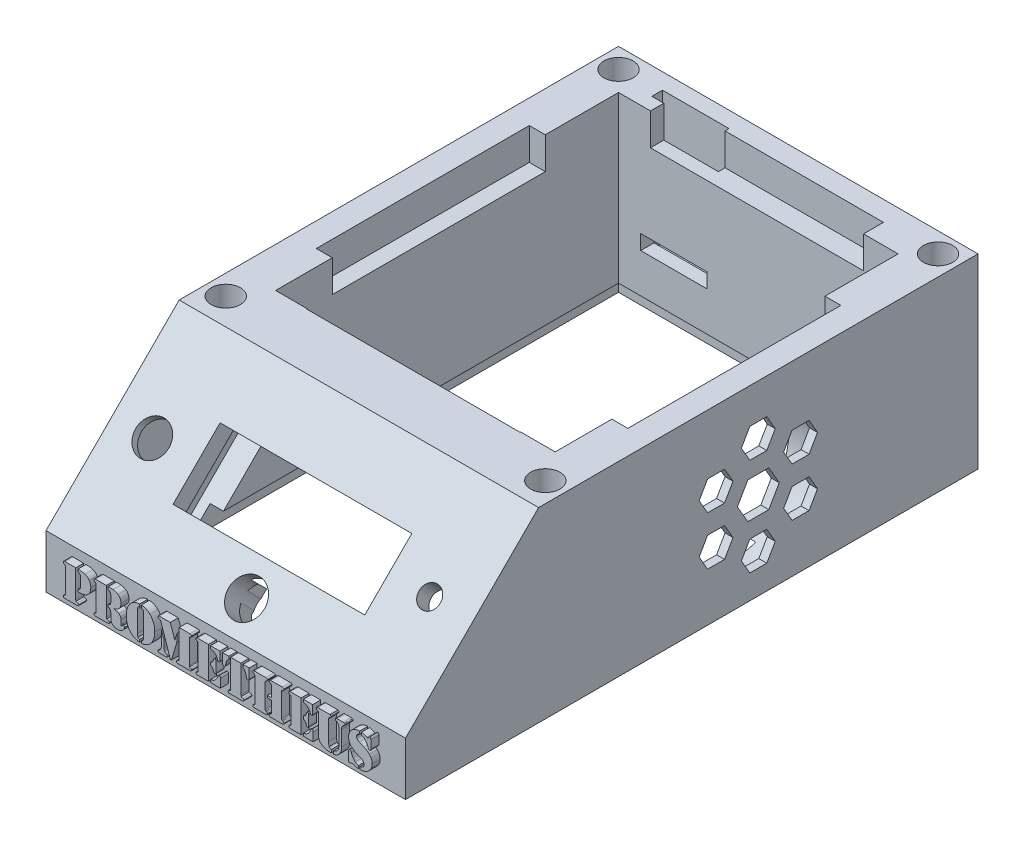
SolidWorks part; units mm, degrees
ref_plane "Front Plane" through (0, 0, 0) normal (0, 0, 1) x (1, 0, 0)
ref_plane "Top Plane" through (0, 0, 0) normal (0, 1, 0) x (1, 0, 0)
ref_plane "Right Plane" through (0, 0, 0) normal (1, 0, 0) x (0, 0, -1)
sketch "Sketch1" plane through (0, 0, 0) normal (0, 1, 0) x (1, 0, 0)
  line L1 (-67.5, -107.5) -> (67.5, -107.5)
  line L2 (-67.5, -107.5) -> (-67.5, 107.5)
  line L3 (-67.5, 107.5) -> (67.5, 107.5)
  line L4 (67.5, -107.5) -> (67.5, 107.5)
  line L5 (-67.5, -107.5) -> (67.5, 107.5) construction
  line L6 (-67.5, 107.5) -> (67.5, -107.5) construction
  point P0 (0, 0)
  dimension "D1" = 135
  dimension "D2" = 215
extrude "Boss-Extrude1" add sketch "Sketch1" along normal blind 70
chamfer "Chamfer1" distance 50 angle 45 1 edges at (0, 70, 107.5)
shell "Shell1" thickness 15
sketch "Sketch2" plane through (0, 0, 0) normal (0, -1, 0) x (-1, 0, 0)
  line L1 (52.5, -91.2868) -> (-52.5, -91.2868)
  line L2 (52.5, -91.2868) -> (52.5, 92.5)
  line L3 (52.5, 92.5) -> (-52.5, 92.5)
  line L4 (-52.5, -91.2868) -> (-52.5, 92.5)
extrude "Cut-Extrude1" cut sketch "Sketch2" against normal blind 15
sketch "Sketch4" plane through (0, 63.75, 63.75) normal (0, 0.7071, 0.7071) x (1, 0, 0)
  line L0 (0, 8.8388) -> (0, -26.4612) construction
  line L1 (-67.5, 8.8388) -> (67.5, 8.8388) construction
  line L2 (0, -26.4612) -> (-67.5, -26.4612) construction
  line L3 (-67.5, -61.8718) -> (-67.5, 8.8388) construction
  line L5 (-36, -13.9612) -> (36, -13.9612)
  line L6 (-36, -13.9612) -> (-36, -38.9612)
  line L7 (-36, -38.9612) -> (36, -38.9612)
  line L8 (36, -13.9612) -> (36, -38.9612)
  line L9 (-36, -13.9612) -> (36, -38.9612) construction
  line L10 (-36, -38.9612) -> (36, -13.9612) construction
  dimension "D1" = 72
  dimension "D2" = 25
extrude "Cut-Extrude2" cut sketch "Sketch4" against normal blind 4.5
sketch "Sketch5" plane through (0, 70, 0) normal (0, 1, 0) x (1, 0, 0)
  line L0 (-60, 107.5) -> (-60, 100) construction
  line L1 (67.5, 107.5) -> (-67.5, 107.5) construction
  line L2 (-60, 100) -> (-67.5, 100) construction
  line L3 (-67.5, 107.5) -> (-67.5, -57.5) construction
  circle A0 centre (-60, 100) radius 5.5
extrude "Cut-Extrude3" cut sketch "Sketch5" against normal blind 15
sketch "Sketch6" plane through (0, 70, 0) normal (0, 1, 0) x (1, 0, 0)
  line L0 (60, 107.5) -> (60, 100) construction
  line L1 (67.5, 107.5) -> (-67.5, 107.5) construction
  line L2 (60, 100) -> (67.5, 100) construction
  line L3 (67.5, -57.5) -> (67.5, 107.5) construction
  circle A0 centre (60, 100) radius 5.5
extrude "Cut-Extrude4" cut sketch "Sketch6" against normal blind 15
sketch "Sketch7" plane through (0, 70, 0) normal (0, 1, 0) x (1, 0, 0)
  line L0 (-67.5, -47.5) -> (-60, -47.5) construction
  line L1 (-67.5, 107.5) -> (-67.5, -57.5) construction
  line L2 (-60, -47.5) -> (-60, -57.5) construction
  line L3 (-67.5, -57.5) -> (67.5, -57.5) construction
  circle A0 centre (-60, -47.5) radius 5.5
extrude "Cut-Extrude5" cut sketch "Sketch7" against normal blind 15
sketch "Sketch8" plane through (0, 70, 0) normal (0, 1, 0) x (1, 0, 0)
  line L0 (67.5, -47.5) -> (60, -47.5) construction
  line L1 (67.5, -57.5) -> (67.5, 107.5) construction
  line L2 (60, -47.5) -> (60, -57.5) construction
  line L3 (-67.5, -57.5) -> (67.5, -57.5) construction
  circle A0 centre (60, -47.5) radius 5.5
extrude "Cut-Extrude6" cut sketch "Sketch8" against normal blind 15
sketch "Sketch9" plane through (0, 63.75, 63.75) normal (0, 0.7071, 0.7071) x (1, 0, 0)
  line L0 (-52.5796, 8.8388) -> (-52.5796, -26.5112) construction
  line L1 (-67.5, 8.8388) -> (67.5, 8.8388) construction
  line L2 (-52.5796, -26.5112) -> (-67.5, -26.5112) construction
  line L3 (-67.5, -61.8718) -> (-67.5, 8.8388) construction
  circle A0 centre (-52.5796, -26.5112) radius 6.25
extrude "Cut-Extrude7" cut sketch "Sketch9" against normal blind 20
sketch "Sketch10" plane through (0, 53.1434, 53.1434) normal (0, -0.7071, -0.7071) x (1, 0, 0)
  line L1 (-61.0796, 44.0112) -> (-44.0796, 44.0112)
  line L2 (-61.0796, 44.0112) -> (-61.0796, 9.0112)
  line L3 (-61.0796, 9.0112) -> (-44.0796, 9.0112)
  line L4 (-44.0796, 44.0112) -> (-44.0796, 9.0112)
  line L5 (-61.0796, 44.0112) -> (-44.0796, 9.0112) construction
  line L6 (-61.0796, 9.0112) -> (-44.0796, 44.0112) construction
  point P0 (-52.5796, 26.5112)
  dimension "D1" = 17
  dimension "D2" = 35
extrude "Cut-Extrude8" cut sketch "Sketch10" along normal blind 30 and the other way blind 12
sketch "Sketch11" plane through (0, 63.75, 63.75) normal (0, 0.7071, 0.7071) x (1, 0, 0)
  line L0 (51.3456, 8.8388) -> (51.3456, -26.1612) construction
  line L1 (-67.5, 8.8388) -> (67.5, 8.8388) construction
  line L2 (51.3456, -26.1612) -> (67.5, -26.1612) construction
  line L3 (67.5, 8.8388) -> (67.5, -61.8718) construction
  circle A0 centre (51.3456, -26.1612) radius 4
extrude "Cut-Extrude9" cut sketch "Sketch11" against normal blind 20
sketch "Sketch13" plane through (0, 53.1434, 53.1434) normal (0, -0.7071, -0.7071) x (1, 0, 0)
  circle A0 centre (51.3456, 26.1612) radius 10
extrude "Cut-Extrude10" cut sketch "Sketch13" along normal blind 10 and the other way blind 8.5
sketch "Sketch16" plane through (0, 53.1434, 53.1434) normal (0, -0.7071, -0.7071) x (1, 0, 0)
  line L17 (-43, 45.9612) -> (-43, 6.9612)
  line L18 (43, 45.9612) -> (-43, 45.9612)
  line L19 (43, 6.9612) -> (43, 45.9612)
  line L20 (-43, 6.9612) -> (43, 6.9612)
  line L21 (-43, 45.9612) -> (-43, 6.9612)
  line L22 (43, 45.9612) -> (-43, 45.9612)
  line L23 (43, 6.9612) -> (43, 45.9612)
  line L24 (-43, 6.9612) -> (43, 6.9612)
  dimension "D1" = 7
extrude "Cut-Extrude13" cut sketch "Sketch16" against normal blind 11
sketch "Sketch20" plane through (0, 53.1434, 53.1434) normal (0, -0.7071, -0.7071) x (-1, 0, 0)
  line L1 (-61.3456, -26.1612) -> (-43, -26.1612)
  line L2 (-61.3456, -26.1612) -> (-61.3456, -0.9057)
  line L3 (-61.3456, -0.9057) -> (-43, -0.9057)
  line L4 (-43, -26.1612) -> (-43, -0.9057)
  arc A0 (-52.5, -16.228) -> (-52.5, -36.0943) centre (-51.3456, -26.1612) ccw construction
extrude "Cut-Extrude14" cut sketch "Sketch20" against normal blind 8.5
sketch "Sketch21" plane through (0, 70, 0) normal (0, 1, 0) x (1, 0, 0)
  line L0 (0, 107.5) -> (0, 25) construction
  line L1 (67.5, 107.5) -> (-67.5, 107.5) construction
  line L2 (0, 25) -> (-67.5, 25) construction
  line L3 (-67.5, 107.5) -> (-67.5, -57.5) construction
  line L5 (-58.5, 65) -> (58.5, 65)
  line L6 (-58.5, 65) -> (-58.5, -15)
  line L7 (-58.5, -15) -> (58.5, -15)
  line L8 (58.5, 65) -> (58.5, -15)
  line L9 (-58.5, 65) -> (58.5, -15) construction
  line L10 (-58.5, -15) -> (58.5, 65) construction
  dimension "D1" = 117
  dimension "D2" = 80
extrude "Cut-Extrude15" cut sketch "Sketch21" against normal blind 12
sketch "Sketch22" plane through (0, 70, 0) normal (0, 1, 0) x (1, 0, 0)
  line L0 (-0.5, 107.5) -> (-0.5, 31.75) construction
  line L1 (67.5, 107.5) -> (-67.5, 107.5) construction
  line L2 (-0.5, 31.75) -> (-67.5, 31.75) construction
  line L3 (-67.5, 107.5) -> (-67.5, -57.5) construction
  line L5 (-40.5, 100) -> (39.5, 100)
  line L6 (-40.5, 100) -> (-40.5, -36.5)
  line L7 (-40.5, -36.5) -> (39.5, -36.5)
  line L8 (39.5, 100) -> (39.5, -36.5)
  line L9 (-40.5, 100) -> (39.5, -36.5) construction
  line L10 (-40.5, -36.5) -> (39.5, 100) construction
  dimension "D1" = 136.5
  dimension "D2" = 80
extrude "Cut-Extrude16" cut sketch "Sketch22" against normal blind 12
sketch "Sketch25" plane through (0, 0, 107.5) normal (0, 0, 1) x (1, 0, 0)
  line L0 (-67.5, 5.1237) -> (8.0252, 5.1237) construction
  line L1 (-67.5, 20) -> (-67.5, 0) construction
  line L2 (8.0252, 5.1237) -> (58.0252, 5.1237) construction
  line L3 (58.0252, 5.1237) -> (58.0252, 20) construction
  line L4 (67.5, 20) -> (-67.5, 20) construction
  text T0 "prometheus" font "Stencil" height 12
extrude "Boss-Extrude2" add sketch "Sketch25" along normal blind 3
sketch "Sketch26" plane through (0, 70, 0) normal (0, 1, 0) x (1, 0, 0)
  line L0 (-32.5, 107.5) -> (-32.5, 99.5) construction
  line L1 (67.5, 107.5) -> (-67.5, 107.5) construction
  line L2 (-32.5, 99.5) -> (-67.5, 99.5) construction
  line L3 (-67.5, 107.5) -> (-67.5, -57.5) construction
  line L5 (-45, 97.5) -> (-20, 97.5)
  line L6 (-45, 97.5) -> (-45, 101.5)
  line L7 (-45, 101.5) -> (-20, 101.5)
  line L8 (-20, 97.5) -> (-20, 101.5)
  line L9 (-45, 97.5) -> (-20, 101.5) construction
  line L10 (-45, 101.5) -> (-20, 97.5) construction
  dimension "D1" = 25
  dimension "D2" = 4
extrude "Cut-Extrude17" cut sketch "Sketch26" against normal blind 50
sketch "Sketch27" plane through (0, 0, -92.5) normal (0, 0, 1) x (1, 0, 0)
  line L1 (-44.1692, 22.7377) -> (-19.2485, 22.7377)
  line L2 (-44.1692, 22.7377) -> (-44.1692, 28.2929)
  line L3 (-44.1692, 28.2929) -> (-19.2485, 28.2929)
  line L4 (-19.2485, 22.7377) -> (-19.2485, 28.2929)
extrude "Cut-Extrude18" cut sketch "Sketch27" against normal blind 5
sketch "Sketch28" plane through (0, 63.75, 63.75) normal (0, 0.7071, 0.7071) x (1, 0, 0)
  line L0 (0, -39.7138) -> (0, -50.8138) construction
  circle A0 centre (0, -50.8138) radius 6.75
extrude "Cut-Extrude19" cut sketch "Sketch28" against normal blind 30
sketch "Sketch29" plane through (0, 53.1434, 53.1434) normal (0, -0.7071, -0.7071) x (1, 0, 0)
  line L1 (-6.5, 57.3138) -> (6.5, 57.3138)
  line L2 (-6.5, 57.3138) -> (-6.5, 44.3138)
  line L3 (-6.5, 44.3138) -> (6.5, 44.3138)
  line L4 (6.5, 57.3138) -> (6.5, 44.3138)
  line L5 (-6.5, 57.3138) -> (6.5, 44.3138) construction
  line L6 (-6.5, 44.3138) -> (6.5, 57.3138) construction
  point P0 (0, 50.8138)
  dimension "D1" = 13
  dimension "D2" = 13
extrude "Cut-Extrude20" cut sketch "Sketch29" against normal blind 7 and the other way blind 10
sketch "Sketch30" plane through (0, 59.1538, 59.1538) normal (0, -0.7071, -0.7071) x (1, 0, 0)
  line L1 (43, 6.9612) -> (61.3456, 6.9612)
  line L2 (43, 6.9612) -> (43, 36.9612)
  line L3 (43, 36.9612) -> (61.3456, 36.9612)
  line L4 (61.3456, 6.9612) -> (61.3456, 36.9612)
  dimension "D1" = 30
  dimension "D2" = 18.3456
extrude "Cut-Extrude21" cut sketch "Sketch30" along normal blind 35
sketch "Sketch31" plane through (0, 60.9216, 60.9216) normal (0, -0.7071, -0.7071) x (1, 0, 0)
  line L1 (-36, 13.9612) -> (-40.8765, 13.9612)
  line L2 (-36, 13.9612) -> (-36, 39.1123)
  line L3 (-36, 39.1123) -> (-40.8765, 39.1123)
  line L4 (-40.8765, 13.9612) -> (-40.8765, 39.1123)
extrude "Boss-Extrude3" add sketch "Sketch31" along normal blind 3
sketch "Sketch33" plane through (52.5, 0, 0) normal (-1, 0, 0) x (0, 0, 1)
  line L0 (-25, 58) -> (-25, 32.9053) construction
  line L1 (15, 58) -> (-65, 58) construction
  circle A0 centre (-25, 32.9053) radius 26.5
extrude "Cut-Extrude22" cut sketch "Sketch33" against normal blind 12
sketch "Sketch34" plane through (64.5, 0, 0) normal (-1, 0, 0) x (0, 0, 1)
  line L1 (-17.1403, 32.9053) -> (-21.0702, 39.712)
  line L2 (-21.0702, 39.712) -> (-28.9298, 39.712)
  line L3 (-28.9298, 39.712) -> (-32.8597, 32.9053)
  line L4 (-32.8597, 32.9053) -> (-28.9298, 26.0986)
  line L5 (-28.9298, 26.0986) -> (-21.0702, 26.0986)
  line L6 (-21.0702, 26.0986) -> (-17.1403, 32.9053)
  circle A0 centre (-25, 32.9053) radius 6.8067 construction
extrude "Cut-Extrude23" cut sketch "Sketch34" against normal blind 12
sketch "Sketch35" plane through (64.5, 0, 0) normal (-1, 0, 0) x (0, 0, 1)
  line L7 (-18.6351, 51.2262) -> (-21.8175, 56.7384)
  line L8 (-21.8175, 56.7384) -> (-28.1825, 56.7384)
  line L9 (-28.1825, 56.7384) -> (-31.3649, 51.2262)
  line L10 (-31.3649, 51.2262) -> (-28.1825, 45.714)
  line L11 (-28.1825, 45.714) -> (-21.8175, 45.714)
  line L12 (-21.8175, 45.714) -> (-18.6351, 51.2262)
  circle A0 centre (-25, 32.9053) radius 7.8597 construction
  circle A1 centre (-25, 51.2262) radius 5.5122 construction
extrude "Cut-Extrude24" cut sketch "Sketch35" against normal blind 12
pattern_circular "CirPattern1" count 6 over 360 about axis through (0, 32.9053, -25) along (1, 0, 0) of "Cut-Extrude24"
sketch "Sketch36" plane through (0, 0, 0) normal (0, -1, 0) x (1, 0, 0)
  line L8 (57.5, -97.5) -> (57.5, 97.5)
  line L9 (57.5, 97.5) -> (-57.5, 97.5)
  line L10 (-57.5, 97.5) -> (-57.5, -97.5)
  line L11 (-57.5, -97.5) -> (57.5, -97.5)
  line L12 (57.5, -97.5) -> (57.5, 97.5)
  line L13 (57.5, 97.5) -> (-57.5, 97.5)
  line L14 (-57.5, 97.5) -> (-57.5, -97.5)
  line L15 (-57.5, -97.5) -> (57.5, -97.5)
  dimension "D1" = 10
extrude "Cut-Extrude25" cut sketch "Sketch36" against normal blind 8
